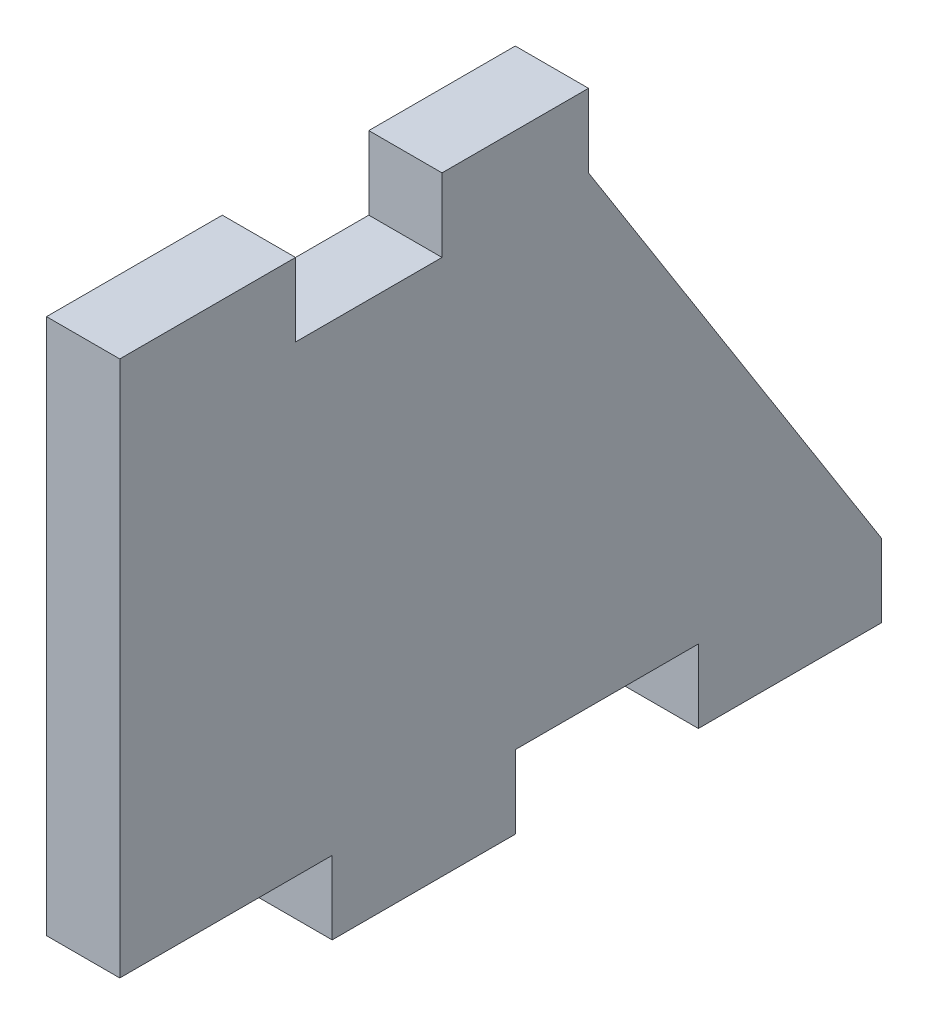
SolidWorks part; units mm, degrees
ref_plane "Front Plane" through (0, 0, 0) normal (0, 0, 1) x (1, 0, 0)
ref_plane "Top Plane" through (0, 0, 0) normal (0, 1, 0) x (1, 0, 0)
ref_plane "Right Plane" through (0, 0, 0) normal (1, 0, 0) x (0, 0, -1)
sketch "Sketch1" plane through (0, 0, 0) normal (1, 0, 0) x (0, 0, -1)
  line L1 (-31.75, -20.066) -> (31.75, -20.066)
  line L2 (-31.75, -20.066) -> (-31.75, 20.066)
  line L3 (-31.75, 20.066) -> (31.75, 20.066)
  line L4 (31.75, -20.066) -> (31.75, 20.066)
  line L5 (-31.75, -20.066) -> (31.75, 20.066) construction
  line L6 (-31.75, 20.066) -> (31.75, -20.066) construction
  point P0 (0, 0)
  dimension "D1" = 40.132
  dimension "D2" = 63.5
extrude "Boss-Extrude1" add sketch "Sketch1" along normal blind 6.35
sketch "Sketch2" plane through (0, 0, 0) normal (-1, 0, 0) x (0, 0, 1)
  line L1 (-31.75, -20.066) -> (-31.75, 20.066)
  line L5 (-31.75, 20.066) -> (31.75, 20.066) construction
  line L18 (-31.75, -20.066) -> (-6.35, 20.066)
  line L19 (-6.35, 20.066) -> (-31.75, 20.066)
extrude "Cut-Extrude1" cut sketch "Sketch2" against normal through all
sketch "Sketch3" plane through (0, 0, 0) normal (-1, 0, 0) x (0, 0, 1)
  line L1 (31.75, 20.066) -> (19.05, 20.066)
  line L2 (31.75, 20.066) -> (31.75, 26.416)
  line L3 (31.75, 26.416) -> (19.05, 26.416)
  line L4 (19.05, 20.066) -> (19.05, 26.416)
  line L5 (-6.35, 20.066) -> (6.35, 20.066)
  line L6 (-6.35, 20.066) -> (-6.35, 26.416)
  line L7 (-6.35, 26.416) -> (6.35, 26.416)
  line L8 (6.35, 20.066) -> (6.35, 26.416)
  line L9 (31.75, -20.066) -> (31.75, -26.416) construction
  line L10 (31.75, -26.416) -> (15.875, -26.416) construction
  line L11 (31.75, -20.066) -> (-31.75, -20.066) construction
  line L12 (15.875, -20.066) -> (0, -20.066)
  line L13 (15.875, -20.066) -> (15.875, -26.416)
  line L14 (15.875, -26.416) -> (0, -26.416)
  line L15 (0, -20.066) -> (0, -26.416)
  line L16 (0, -26.416) -> (-15.875, -26.416) construction
  line L17 (6.35, 26.416) -> (19.05, 26.416) construction
  line L18 (-31.75, -20.066) -> (-15.875, -20.066)
  line L19 (-31.75, -20.066) -> (-31.75, -26.416)
  line L20 (-31.75, -26.416) -> (-15.875, -26.416)
  line L21 (-15.875, -20.066) -> (-15.875, -26.416)
  dimension "D2" = 6.35
extrude "Boss-Extrude2" add sketch "Sketch3" against normal through all
sketch "Sketch4" plane through (0, 0, 0) normal (-1, 0, 0) x (0, 0, 1)
  line L2 (31.75, 26.416) -> (31.75, -20.066) construction
  line L3 (31.75, -15.875) -> (29.21, -15.875)
  line L4 (31.75, -15.875) -> (31.75, 21.209)
  line L5 (31.75, 21.209) -> (29.21, 21.209)
  line L6 (29.21, -15.875) -> (29.21, 21.209)
  dimension "D1" = 2.54
extrude "Boss-Extrude7" add sketch "Sketch4" against normal blind 6.35
sketch "Sketch6" plane through (6.35, 0, 0) normal (1, 0, 0) x (0, 0, -1)
  line L1 (-31.75, 26.416) -> (-34.29, 26.416)
  line L2 (-31.75, 26.416) -> (-31.75, -20.066)
  line L3 (-31.75, -20.066) -> (-34.29, -20.066)
  line L4 (-34.29, 26.416) -> (-34.29, -20.066)
extrude "Boss-Extrude8" add sketch "Sketch6" against normal blind 6.35
equation "\"D1@Boss-Extrude1\" = \"material\""
equation "\"D1@Boss-Extrude7\"=\"material\""
equation "\"material\"=\"GMaterial@Platform.assembly\""
equation "\"D2@Sketch3\" = \"material\""
equation "\"D1@Sketch4\"=\"Acrylic\""
equation "\"Acrylic\"=\"Acrylic@Platform.assembly\""
equation "\"D1@Boss-Extrude8\"=\"material\""
